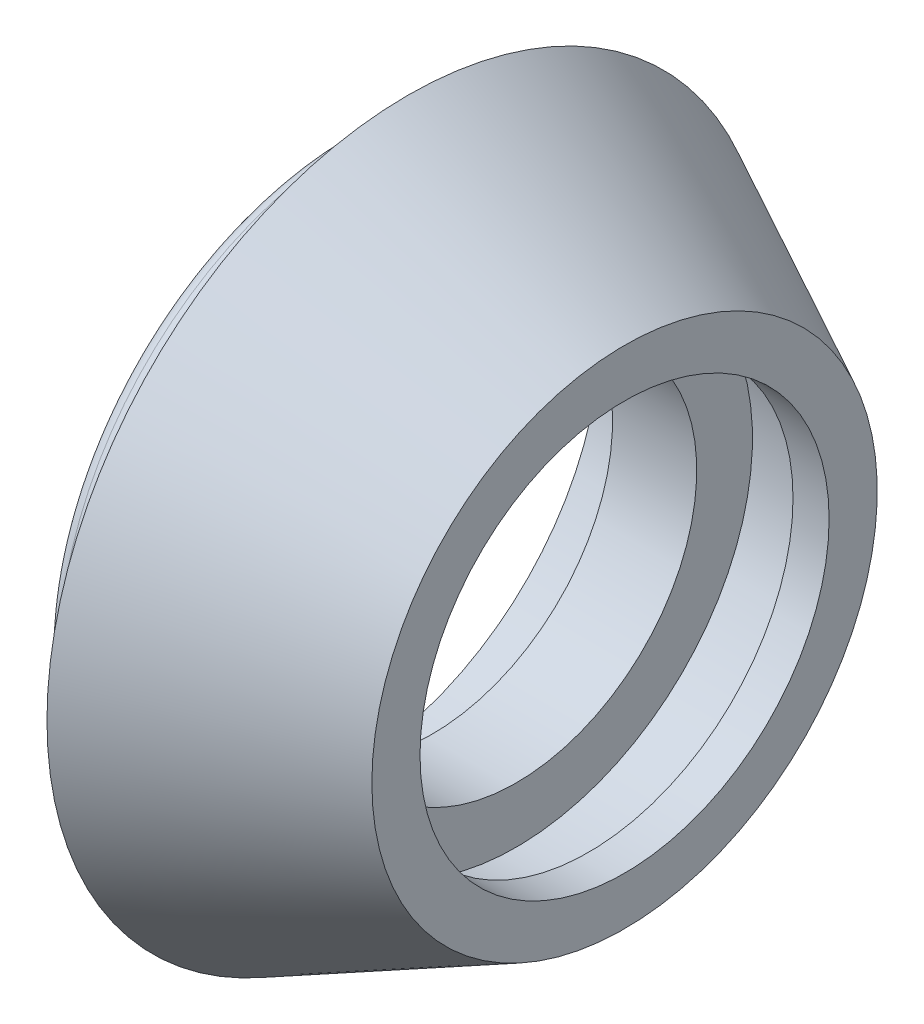
SolidWorks part; units mm, degrees
ref_plane "Plan de face" through (0, 0, 0) normal (0, 0, 1) x (1, 0, 0)
ref_plane "Plan de dessus" through (0, 0, 0) normal (0, 1, 0) x (1, 0, 0)
ref_plane "Plan de droite" through (0, 0, 0) normal (1, 0, 0) x (0, 0, -1)
sketch "Esquisse1" plane through (0, 0, 0) normal (0, 0, 1) x (1, 0, 0)
  line L0 (-27.6063, 0) -> (28.7486, 0) construction
  line L1 (-8, 7.5) -> (-4.5, 7.5)
  line L2 (-4.5, 7.5) -> (-4.5, 9.815)
  line L3 (-4.5, 9.815) -> (-1.5, 9.815)
  line L4 (-1.5, 9.815) -> (-1.5, 8.5)
  line L5 (-1.5, 8.5) -> (0, 8.5)
  line L6 (0, 8.5) -> (0, 10.5)
  line L7 (0, 10.5) -> (-9, 15)
  line L8 (-9, 15) -> (-9, 12)
  line L9 (-9, 12) -> (-10.5, 12)
  line L10 (-10.5, 12) -> (-10.5, 12.5)
  line L11 (-10.5, 12.5) -> (-11.5, 12.5)
  line L12 (-11.5, 12.5) -> (-11.5, 10.5)
  line L13 (-11.5, 10.5) -> (-8, 10.5)
  line L14 (-8, 7.5) -> (-8, 10.5)
  dimension "D1" = 15
  dimension "D2" = 19.63
  dimension "D3" = 17
  dimension "D4" = 3
  dimension "D5" = 1.5
  dimension "D6" = 3.5
  dimension "D7" = 21
  dimension "D8" = 9
  dimension "D9" = 30
  dimension "D10" = 1
  dimension "D11" = 11.5
  dimension "D12" = 24
  dimension "D13" = 21
  dimension "D14" = 25
revolve "Révolution1" add sketch "Esquisse1" angle 360 about L0
fillet "Congé1" radius 0.5 1 edges at (-11.5, 0, 12.5)
